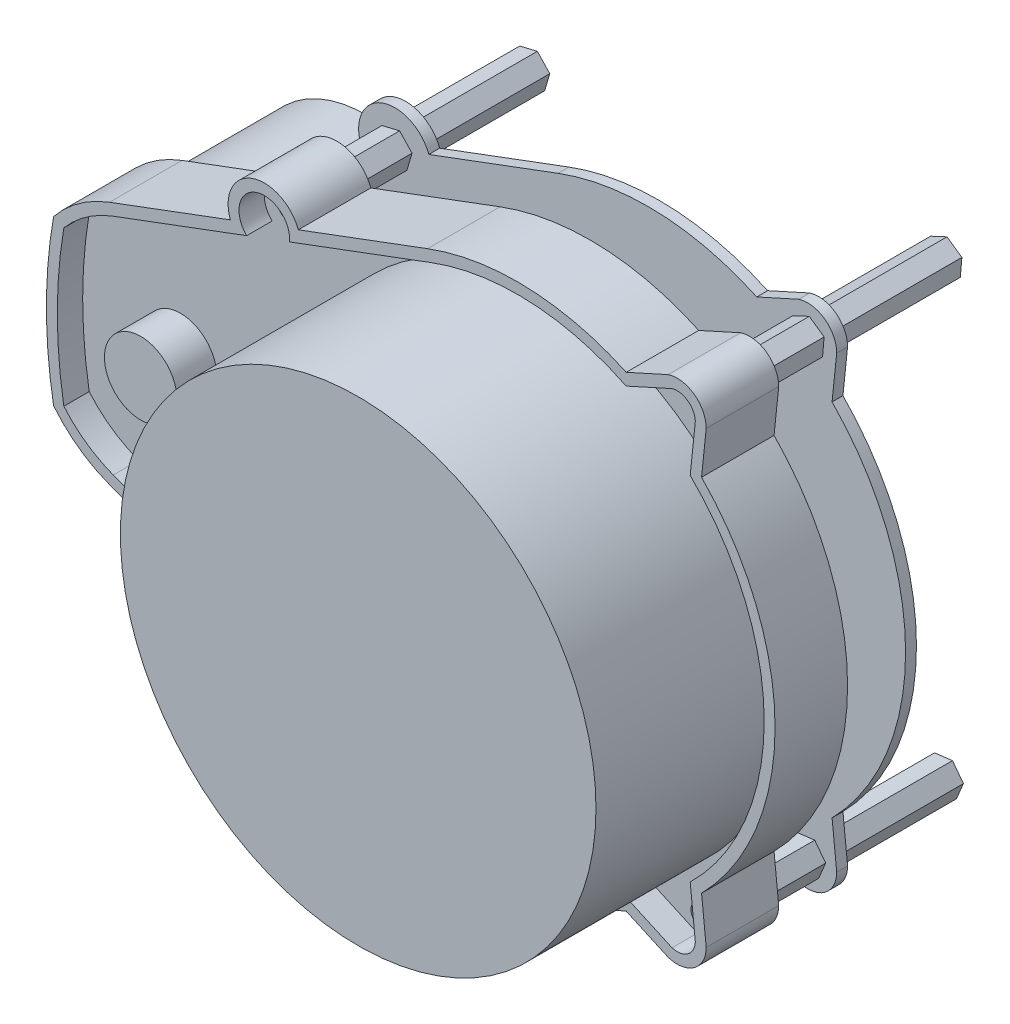
SolidWorks part; units mm, degrees
ref_plane "Plan de face" through (0, 0, 0) normal (0, 0, 1) x (1, 0, 0)
ref_plane "Plan de dessus" through (0, 0, 0) normal (0, 1, 0) x (1, 0, 0)
ref_plane "Plan de droite" through (0, 0, 0) normal (1, 0, 0) x (0, 0, -1)
sketch "Esquisse1" plane through (0, 0, 0) normal (0, 0, 1) x (1, 0, 0)
  line L0 (-12.425, 33.2546) -> (-30.2572, 26.5919)
  line L1 (-56.3, 16.8615) -> (-56.3, -16.8615) construction
  line L2 (-50, 0) -> (0, 0) construction
  line L3 (-12.425, 33.2546) -> (-12.425, -33.2546) construction
  line L5 (-35, 25) -> (-34.9409, 24.8419) construction
  line L6 (-39.6247, 23.0919) -> (-56.3, 16.8615)
  line L7 (-33.4505, 25.3988) -> (-36.4314, 24.2851)
  line L8 (20.756, 34.8016) -> (14.974, 32.1874)
  line L9 (26, 31) -> (25.36, 24.8419)
  line L10 (-65, 0) -> (35.5, 0) construction
  line L11 (55, 0) -> (-55, 0) construction
  line L12 (-35, -25) -> (-34.9409, -24.8419) construction
  line L13 (26, -31) -> (25.36, -24.8419)
  line L14 (20.756, -34.8016) -> (14.974, -32.1874)
  line L15 (-33.4505, -25.3988) -> (-36.4314, -24.2851)
  line L16 (-39.6247, -23.0919) -> (-56.3, -16.8615)
  line L17 (-12.425, -33.2546) -> (-30.2572, -26.5919)
  arc A1 (25.36, -24.8419) -> (25.36, 24.8419) centre (0, 0) ccw
  arc A3 (-64.01, 11.3013) -> (-64.01, -11.3013) centre (0, 0) ccw
  arc A4 (-56.3, 16.8615) -> (-64.01, 11.3013) centre (-50, 0) ccw
  circle A5 centre (22, 31) radius 1.6
  circle A6 centre (-35, 25) radius 1.6
  arc A7 (-30.2572, 26.5919) -> (-39.6247, 23.0919) centre (-34.9409, 24.8419) ccw
  arc A8 (26, 31) -> (20.756, 34.8016) centre (22, 31) ccw
  arc A9 (14.974, 32.1874) -> (-12.425, 33.2546) centre (0, 0) ccw
  arc A10 (14.974, -32.1874) -> (-12.425, -33.2546) centre (0, 0) cw
  arc A11 (26, -31) -> (20.756, -34.8016) centre (22, -31) cw
  arc A12 (-30.2572, -26.5919) -> (-39.6247, -23.0919) centre (-34.9409, -24.8419) cw
  circle A13 centre (-35, -25) radius 1.6
  circle A14 centre (22, -31) radius 1.6
  arc A15 (-56.3, -16.8615) -> (-64.01, -11.3013) centre (-50, 0) cw
  point P28 (-12.425, 0)
  point P29 (-56.3, 0)
  dimension "D1" = 71
  dimension "D4" = 130
  dimension "D6" = 3.2
  dimension "D10" = 10
  dimension "D11" = 8
  dimension "D3" = 50
  dimension "D5" = 31
  dimension "D7" = 22
  dimension "D8" = 35
  dimension "D9" = 25
extrude "Boss.-Extru.1" add sketch "Esquisse1" along normal blind 10 contours A15 L16 A12 L17 A10 L14 A11 L13 A1 L9 A8 L8 A9 L0 A7 L6 A4 A3 A13 A5 A6 A14
sketch "Esquisse2" plane through (0, 0, 10) normal (0, 0, 1) x (1, 0, 0)
  circle A0 centre (0, 0) radius 32.8
  dimension "D1" = 65.6
extrude "Boss.-Extru.2" add sketch "Esquisse2" along normal blind 22
sketch "Esquisse3" plane through (0, 0, 10) normal (0, 0, 1) x (1, 0, 0)
  line L16 (-55.775, -15.4564) -> (-37.3782, -22.33)
  line L17 (14.9568, -30.5335) -> (21.2911, -33.3974)
  line L18 (24.4991, -31.0687) -> (23.7942, -24.2866)
  line L19 (23.7942, 24.2866) -> (24.4991, 31.0687)
  line L20 (21.2911, 33.3974) -> (14.9568, 30.5335)
  line L21 (-11.9, 31.8495) -> (-31.4537, 24.5436)
  line L22 (-55.775, -15.4564) -> (-37.3782, -22.33)
  line L23 (14.9568, -30.5335) -> (21.2911, -33.3974)
  line L24 (24.4991, -31.0687) -> (23.7942, -24.2866)
  line L25 (23.7942, 24.2866) -> (24.4991, 31.0687)
  line L26 (21.2911, 33.3974) -> (14.9568, 30.5335)
  line L27 (-11.9, 31.8495) -> (-31.4537, 24.5436)
  line L28 (-31.4537, -24.5436) -> (-11.9, -31.8495)
  line L29 (-31.4537, -24.5436) -> (-11.9, -31.8495)
  line L30 (-37.3782, 22.33) -> (-55.775, 15.4564)
  line L31 (-37.3782, 22.33) -> (-55.775, 15.4564)
  arc A20 (-62.6, -10.6532) -> (-55.775, -15.4564) centre (-50, 0) ccw
  arc A21 (-11.9, -31.8495) -> (14.9568, -30.5335) centre (0, 0) ccw
  arc A22 (23.7942, -24.2866) -> (23.7942, 24.2866) centre (0, 0) ccw
  arc A23 (14.9568, 30.5335) -> (-11.9, 31.8495) centre (0, 0) ccw
  arc A24 (-55.775, 15.4564) -> (-62.6, 10.6532) centre (-50, 0) ccw
  arc A25 (-62.6, 10.6532) -> (-62.6, -10.6532) centre (0, 0) ccw
  arc A26 (-62.6, -10.6532) -> (-55.775, -15.4564) centre (-50, 0) ccw
  arc A27 (-11.9, -31.8495) -> (14.9568, -30.5335) centre (0, 0) ccw
  arc A28 (23.7942, -24.2866) -> (23.7942, 24.2866) centre (0, 0) ccw
  arc A29 (14.9568, 30.5335) -> (-11.9, 31.8495) centre (0, 0) ccw
  arc A30 (-55.775, 15.4564) -> (-62.6, 10.6532) centre (-50, 0) ccw
  arc A31 (-62.6, 10.6532) -> (-62.6, -10.6532) centre (0, 0) ccw
  arc A32 (-37.3782, -22.33) -> (-31.4537, -24.5436) centre (-34.9409, -24.8419) ccw
  arc A33 (-37.3782, -22.33) -> (-31.4537, -24.5436) centre (-34.9409, -24.8419) ccw
  arc A34 (21.2911, -33.3974) -> (24.4991, -31.0687) centre (22, -31) ccw
  arc A35 (21.2911, -33.3974) -> (24.4991, -31.0687) centre (22, -31) ccw
  arc A36 (24.4991, 31.0687) -> (21.2911, 33.3974) centre (22, 31) ccw
  arc A37 (24.4991, 31.0687) -> (21.2911, 33.3974) centre (22, 31) ccw
  arc A38 (-31.4537, 24.5436) -> (-37.3782, 22.33) centre (-34.9409, 24.8419) ccw
  arc A39 (-31.4537, 24.5436) -> (-37.3782, 22.33) centre (-34.9409, 24.8419) ccw
  dimension "D1" = 1.5
extrude "Enlèv. mat.-Extru.1" cut sketch "Esquisse3" against normal blind 3.5
sketch "Esquisse4" plane through (0, 0, 10) normal (0, 0, -1) x (-1, 0, 0)
  circle A1 centre (0, 0) radius 32.8
  circle A2 centre (0, 0) radius 32.8
  dimension "D1" = 0
extrude "Boss.-Extru.3" add sketch "Esquisse4" along normal up to next
sketch "Esquisse5" plane through (0, 0, 0) normal (0, 0, -1) x (-1, 0, 0)
  circle A0 centre (50, 0) radius 16
  dimension "D2" = 32
  dimension "D1" = 50
extrude "Boss.-Extru.4" add sketch "Esquisse5" along normal blind 19
sketch "Esquisse6" plane through (0, 0, 0) normal (0, 0, -1) x (-1, 0, 0)
  line L1 (-20.4892, -29.0081) -> (-22.9696, -28.6957)
  line L2 (-22.9696, -28.6957) -> (-24.4804, -30.6876)
  line L3 (-24.4804, -30.6876) -> (-23.5108, -32.9919)
  line L4 (-23.5108, -32.9919) -> (-21.0304, -33.3043)
  line L5 (-21.0304, -33.3043) -> (-19.5196, -31.3124)
  line L6 (-19.5196, -31.3124) -> (-20.4892, -29.0081)
  line L7 (36.0868, -22.7486) -> (33.5937, -22.9331)
  line L8 (33.5937, -22.9331) -> (32.5068, -25.1845)
  line L9 (32.5068, -25.1845) -> (33.9132, -27.2514)
  line L10 (33.9132, -27.2514) -> (36.4063, -27.0669)
  line L11 (36.4063, -27.0669) -> (37.4932, -24.8155)
  line L12 (37.4932, -24.8155) -> (36.0868, -22.7486)
  line L13 (36.7203, 26.814) -> (34.2892, 27.3968)
  line L14 (34.2892, 27.3968) -> (32.5689, 25.5828)
  line L15 (32.5689, 25.5828) -> (33.2797, 23.186)
  line L16 (33.2797, 23.186) -> (35.7108, 22.6032)
  line L17 (35.7108, 22.6032) -> (37.4311, 24.4172)
  line L18 (37.4311, 24.4172) -> (36.7203, 26.814)
  line L19 (-19.9522, 32.434) -> (-22.218, 33.4905)
  line L20 (-22.218, 33.4905) -> (-24.2658, 32.0565)
  line L21 (-24.2658, 32.0565) -> (-24.0478, 29.566)
  line L22 (-24.0478, 29.566) -> (-21.782, 28.5095)
  line L23 (-21.782, 28.5095) -> (-19.7342, 29.9435)
  line L24 (-19.7342, 29.9435) -> (-19.9522, 32.434)
  circle A0 centre (-22, -31) radius 2.1651 construction
  circle A1 centre (35, -25) radius 2.1651 construction
  circle A2 centre (35, 25) radius 2.1651 construction
  circle A3 centre (-22, 31) radius 2.1651 construction
  circle A4 centre (35, -25) radius 1
  circle A5 centre (35, 25) radius 1
  circle A6 centre (-22, 31) radius 1
  circle A7 centre (-22, -31) radius 1
  dimension "D2" = 2
  dimension "D1" = 5
extrude "Boss.-Extru.5" add sketch "Esquisse6" along normal blind 27
ref_plane "Plan1" through (0, 0, -8) normal (0, 0, -1) x (-1, 0, 0)
sketch "Esquisse7" plane through (0, 0, -8) normal (0, 0, -1) x (-1, 0, 0)
  line L0 (50, 0) -> (80, 0) construction
  line L8 (56.3, 16.8615) -> (39.6247, 23.0919)
  line L9 (30.2572, 26.5919) -> (12.425, 33.2546)
  line L10 (-14.974, 32.1874) -> (-20.756, 34.8016)
  line L11 (-26, 31) -> (-25.36, 24.8419)
  line L12 (-25.36, -24.8419) -> (-26, -31)
  line L13 (-20.756, -34.8016) -> (-14.974, -32.1874)
  line L14 (12.425, -33.2546) -> (30.2572, -26.5919)
  line L15 (39.6247, -23.0919) -> (56.3, -16.8615)
  line L17 (30.2572, 26.5919) -> (12.425, 33.2546)
  line L18 (-14.974, 32.1874) -> (-20.756, 34.8016)
  line L19 (-26, 31) -> (-25.36, 24.8419)
  line L20 (-25.36, -24.8419) -> (-26, -31)
  line L21 (-20.756, -34.8016) -> (-14.974, -32.1874)
  line L22 (12.425, -33.2546) -> (30.2572, -26.5919)
  arc A0 (39.6247, 23.0919) -> (39.6247, -23.0919) centre (80, 0) ccw
  arc A12 (64.69, 6.3407) -> (64.69, -6.3407) centre (50, 0) ccw
  arc A13 (64.69, 6.3407) -> (64.01, 11.3013) centre (0, 0) ccw
  arc A14 (64.01, 11.3013) -> (56.3, 16.8615) centre (50, 0) ccw
  arc A15 (39.6247, 23.0919) -> (30.2572, 26.5919) centre (34.9409, 24.8419) ccw
  arc A16 (12.425, 33.2546) -> (-14.974, 32.1874) centre (0, 0) ccw
  arc A17 (-20.756, 34.8016) -> (-26, 31) centre (-22, 31) ccw
  arc A18 (-25.36, 24.8419) -> (-25.36, -24.8419) centre (0, 0) ccw
  arc A19 (-26, -31) -> (-20.756, -34.8016) centre (-22, -31) ccw
  arc A20 (-14.974, -32.1874) -> (12.425, -33.2546) centre (0, 0) ccw
  arc A21 (30.2572, -26.5919) -> (39.6247, -23.0919) centre (34.9409, -24.8419) ccw
  arc A22 (56.3, -16.8615) -> (64.01, -11.3013) centre (50, 0) ccw
  arc A23 (64.01, -11.3013) -> (64.69, -6.3407) centre (0, 0) ccw
  arc A27 (39.6247, 23.0919) -> (30.2572, 26.5919) centre (34.9409, 24.8419) ccw
  arc A28 (12.425, 33.2546) -> (-14.974, 32.1874) centre (0, 0) ccw
  arc A29 (-20.756, 34.8016) -> (-26, 31) centre (-22, 31) ccw
  arc A30 (-25.36, 24.8419) -> (-25.36, -24.8419) centre (0, 0) ccw
  arc A31 (-26, -31) -> (-20.756, -34.8016) centre (-22, -31) ccw
  arc A32 (-14.974, -32.1874) -> (12.425, -33.2546) centre (0, 0) ccw
  arc A33 (30.2572, -26.5919) -> (39.6247, -23.0919) centre (34.9409, -24.8419) ccw
  dimension "D2" = 30
  dimension "D1" = 0
extrude "Boss.-Extru.6" add sketch "Esquisse7" along normal blind 1.5
sketch "Esquisse8" plane through (0, 0, 6.5) normal (0, 0, 1) x (1, 0, 0)
  circle A0 centre (-50, 0) radius 5
  dimension "D1" = 10
extrude "Boss.-Extru.7" add sketch "Esquisse8" along normal blind 5.5
